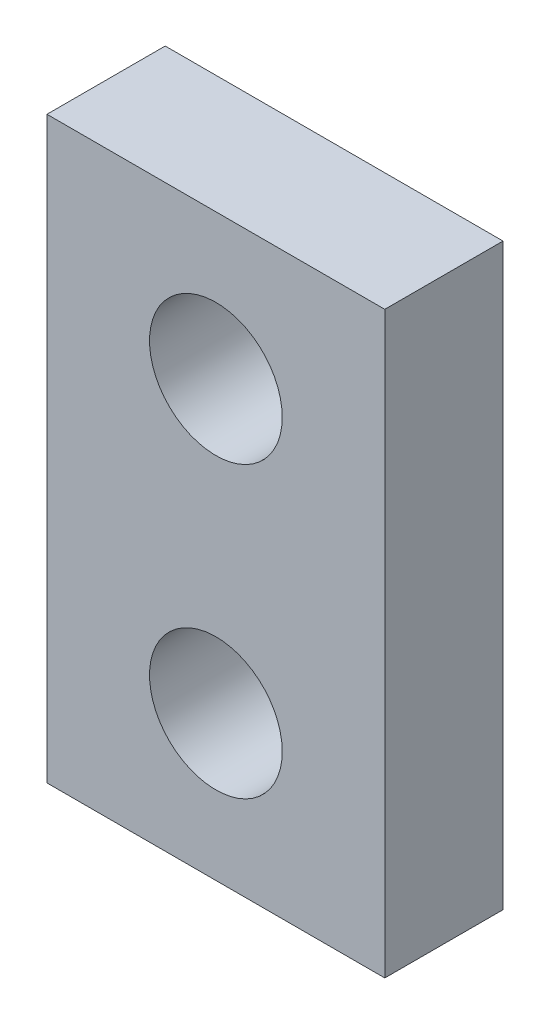
SolidWorks part; units mm, degrees
ref_plane "Front" through (0, 0, 0) normal (0, 0, 1) x (1, 0, 0)
ref_plane "Top" through (0, 0, 0) normal (0, 1, 0) x (1, 0, 0)
ref_plane "Right" through (0, 0, 0) normal (1, 0, 0) x (0, 0, -1)
sketch "Sketch1" plane through (0, 0, 0) normal (0, 0, 1) x (1, 0, 0)
  line L1 (0, 0) -> (7, 0)
  line L2 (0, 0) -> (0, 12)
  line L3 (0, 12) -> (7, 12)
  line L4 (7, 0) -> (7, 12)
  circle A0 centre (3.5, 3) radius 1.375
  circle A1 centre (3.5, 9) radius 1.375
  dimension "D1" = 2.75
  dimension "D2" = 6
  dimension "D3" = 12
  dimension "D4" = 3
  dimension "D5" = 3.5
  dimension "D6" = 3.5
extrude "rearTailLightSpacer" add sketch "Sketch1" along normal blind 2.45
